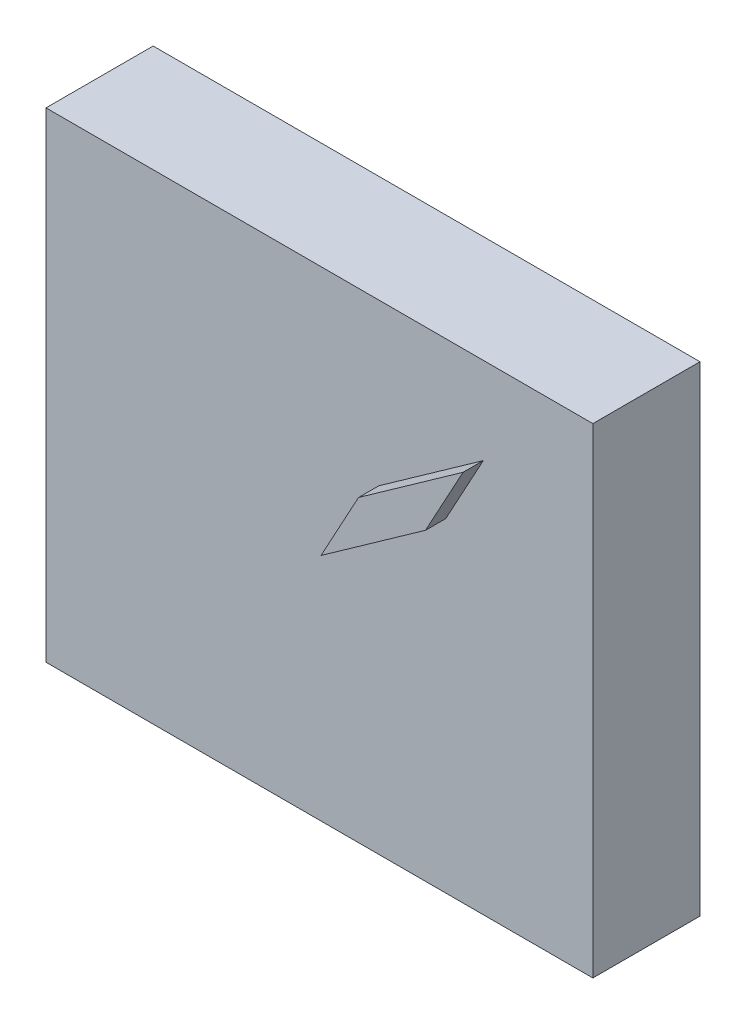
SolidWorks part; units mm, degrees
ref_plane "正面" through (0, 0, 0) normal (0, 0, 1) x (1, 0, 0)
ref_plane "平面" through (0, 0, 0) normal (0, 1, 0) x (1, 0, 0)
ref_plane "右側面" through (0, 0, 0) normal (1, 0, 0) x (0, 0, -1)
sketch "ｽｹｯﾁ1" plane through (0, 0, 0) normal (0, 0, 1) x (1, 0, 0)
  line L1 (0, 0) -> (54.1, 0)
  line L2 (0, 0) -> (0, 47.5)
  line L3 (0, 47.5) -> (54.1, 47.5)
  line L4 (54.1, 0) -> (54.1, 47.5)
  dimension "D1" = 54.1
  dimension "D2" = 47.5
extrude "ﾎﾞｽ - 押し出し1" add sketch "ｽｹｯﾁ1" along normal blind 10.6
sketch "ｽｹｯﾁ2" plane through (0, 0, 10.6) normal (0, 0, 1) x (1, 0, 0)
  line L0 (43.2594, 38.9074) -> (32.9203, 31.5796)
  line L1 (43.2594, 38.9074) -> (39.5454, 32.0815)
  line L2 (32.9203, 31.5796) -> (29.2063, 24.7538)
  line L3 (39.5454, 32.0815) -> (29.2063, 24.7538)
extrude "ﾎﾞｽ - 押し出し2" add sketch "ｽｹｯﾁ2" along normal blind 2
